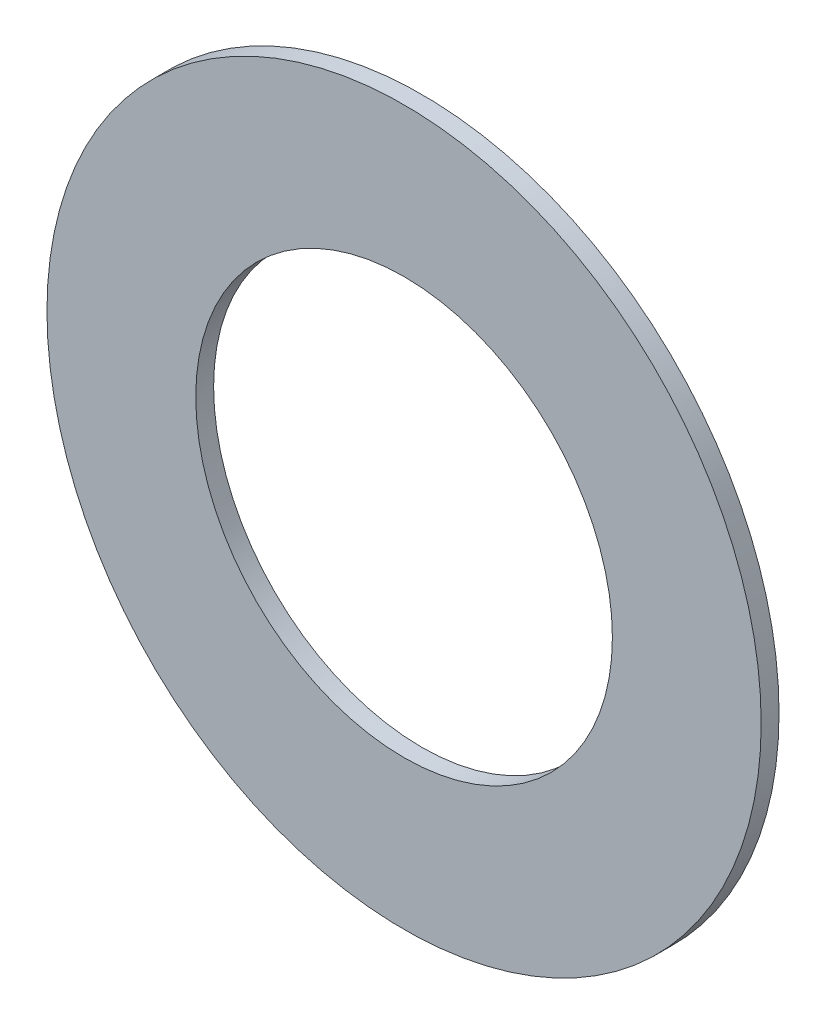
SolidWorks part; units mm, degrees
ref_plane "Alzado" through (0, 0, 0) normal (0, 0, 1) x (1, 0, 0)
ref_plane "Planta" through (0, 0, 0) normal (0, 1, 0) x (1, 0, 0)
ref_plane "Vista lateral" through (0, 0, 0) normal (1, 0, 0) x (0, 0, -1)
sketch "Croquis1" plane through (0, 0, 0) normal (0, 0, 1) x (1, 0, 0)
  circle A0 centre (0, 0) radius 6
  circle A1 centre (0, 0) radius 3.5
  dimension "D1" = 7
  dimension "D2" = 12
extrude "Saliente-Extruir1" add sketch "Croquis1" along normal blind 0.3
